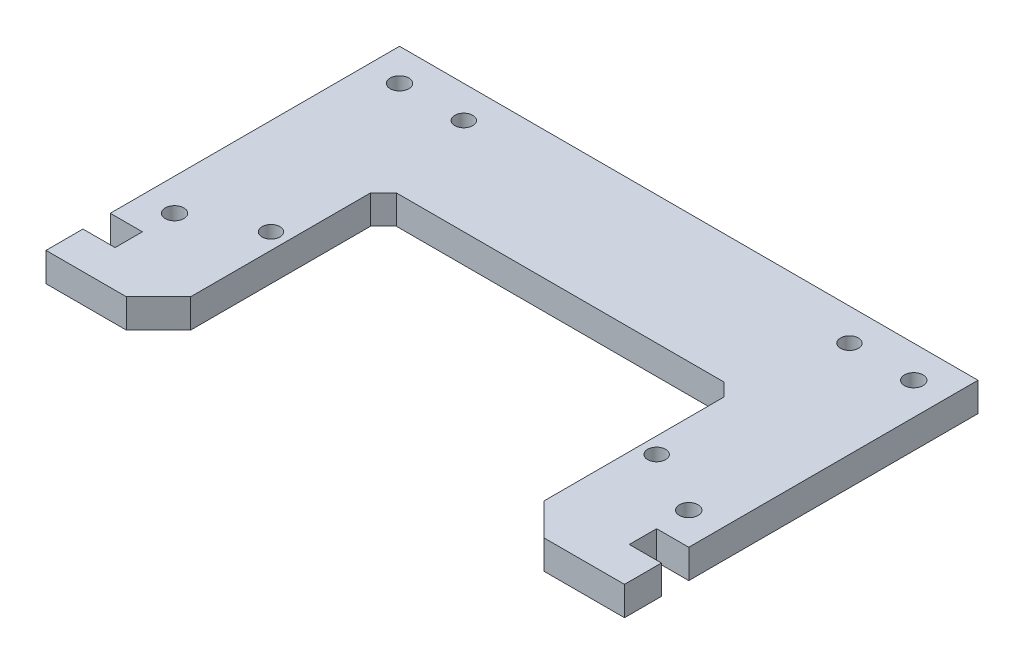
SolidWorks part; units mm, degrees
ref_plane "Front Plane" through (0, 0, 0) normal (0, 0, 1) x (1, 0, 0)
ref_plane "Top Plane" through (0, 0, 0) normal (0, 1, 0) x (1, 0, 0)
ref_plane "Right Plane" through (0, 0, 0) normal (1, 0, 0) x (0, 0, -1)
sketch "Sketch1" plane through (0, 0, 0) normal (0, 1, 0) x (1, 0, 0)
  line L1 (-45, 0) -> (45, 0)
  line L2 (-45, 0) -> (-45, -55)
  line L3 (-45, -55) -> (45, -55)
  line L4 (45, 0) -> (45, -55)
  line L5 (-40, -40) -> (40, -40) construction
  line L6 (-40, -40) -> (-40, -5) construction
  line L7 (-40, -5) -> (40, -5) construction
  line L8 (40, -40) -> (40, -5) construction
  circle A0 centre (-40, -40) radius 1.45
  circle A1 centre (-40, -5) radius 1.45
  circle A2 centre (40, -40) radius 1.45
  circle A3 centre (40, -5) radius 1.45
  dimension "D3" = 5
  dimension "D5" = 2.9
  dimension "D1" = 90
  dimension "D2" = 55
  dimension "D4" = 15
  dimension "D6" = 5
  dimension "D7" = 5
extrude "Boss-Extrude1" add sketch "Sketch1" along normal blind 4.5
sketch "Sketch2" plane through (0, 4.5, 0) normal (0, 1, 0) x (1, 0, 0)
  line L0 (0, -20) -> (0, 0) construction
  line L1 (27.5, -55) -> (-27.5, -55)
  line L2 (27.5, -55) -> (27.5, -20)
  line L3 (27.5, -20) -> (-27.5, -20)
  line L4 (-27.5, -55) -> (-27.5, -20)
  line L5 (-45, -55) -> (45, -55) construction
  dimension "D1" = 55
  dimension "D2" = 20
extrude "Cut-Extrude1" cut sketch "Sketch2" against normal through all
sketch "Sketch3" plane through (0, 4.5, 0) normal (0, 1, 0) x (1, 0, 0)
  line L0 (-45, 0) -> (-45, -55) construction
  line L1 (-45, -49.25) -> (-40, -49.25)
  line L2 (-45, -49.25) -> (-45, -45)
  line L3 (-45, -45) -> (-40, -45)
  line L4 (-40, -49.25) -> (-40, -45)
  line L5 (45, -55) -> (45, 0) construction
  line L6 (45, -45) -> (40, -45)
  line L7 (45, -45) -> (45, -49.25)
  line L8 (45, -49.25) -> (40, -49.25)
  line L9 (40, -45) -> (40, -49.25)
  line L10 (45, 0) -> (-45, 0) construction
  dimension "D1" = 4.25
  dimension "D2" = 5
  dimension "D3" = 45
extrude "Cut-Extrude2" cut sketch "Sketch3" against normal through all
sketch "Sketch4" plane through (0, 4.5, 0) normal (0, 1, 0) x (1, 0, 0)
  circle A0 centre (-30, -35) radius 1.4
  circle A1 centre (-30, -5) radius 1.4
  point P2 (-40, -40)
  point P7 (-40, -5)
  dimension "D1" = 2.8
  dimension "D2" = 30
  dimension "D3" = 30
extrude "Cut-Extrude3" cut sketch "Sketch4" against normal through all
mirror "Mirror1" about plane through (0, 0, 0) normal (1, 0, 0) of "Cut-Extrude3"
chamfer "Chamfer1" distance 5 angle 45 2 edges at (27.5, 2.25, 55) (-27.5, 2.25, 55)
chamfer "Chamfer2" distance 2 angle 45 2 edges at (27.5, 2.25, 20) (-27.5, 2.25, 20)
